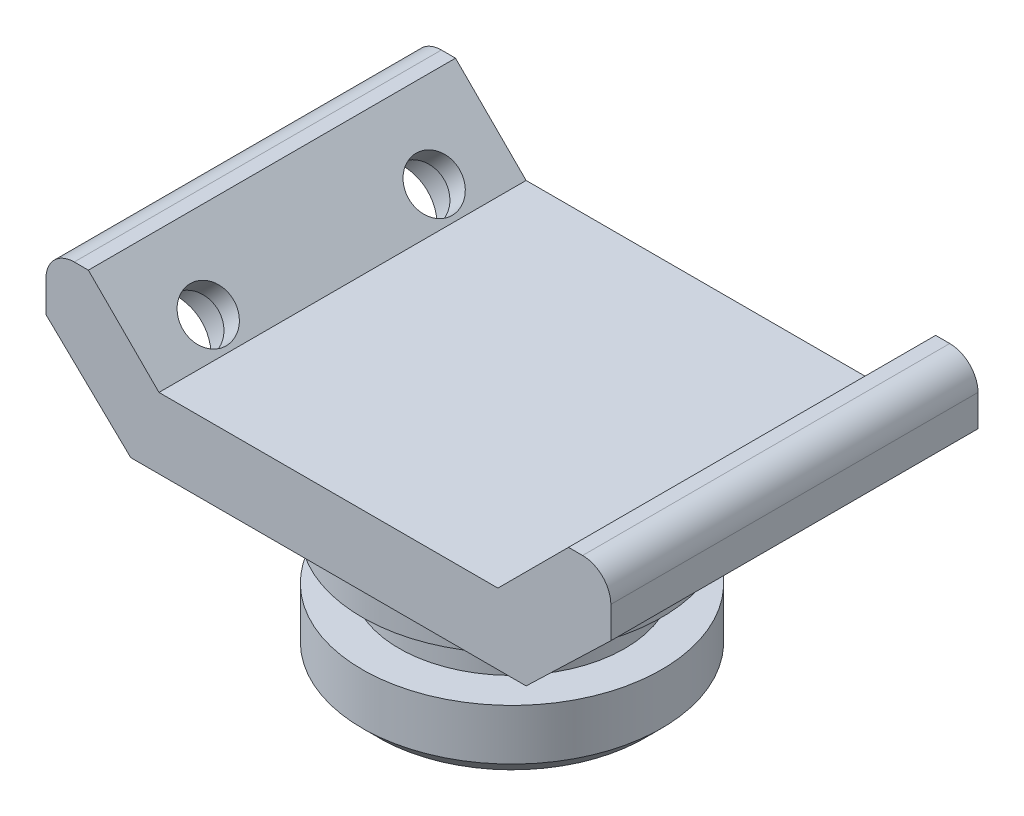
SolidWorks part; units mm, degrees
ref_plane "Alzado" through (0, 0, 0) normal (0, 0, 1) x (1, 0, 0)
ref_plane "Planta" through (0, 0, 0) normal (0, 1, 0) x (1, 0, 0)
ref_plane "Vista lateral" through (0, 0, 0) normal (1, 0, 0) x (0, 0, -1)
sketch "Sketch1" plane through (0, 0, 0) normal (0, 0, 1) x (1, 0, 0)
  line L0 (0, 0) -> (0, 47.9033) construction
  line L1 (-35, 0) -> (35, 0)
  line L2 (35, 0) -> (50, 14.4247)
  line L3 (50, 14.4247) -> (50, 25)
  line L4 (50, 25) -> (42.5, 25)
  line L5 (42.5, 25) -> (30, 12.5)
  line L6 (30, 12.5) -> (-30, 12.5)
  line L7 (-42.5, 25) -> (-30, 12.5)
  line L8 (-50, 25) -> (-42.5, 25)
  line L9 (-50, 14.4247) -> (-50, 25)
  line L10 (-35, 0) -> (-50, 14.4247)
  point P10 (0, 12.5)
  dimension "D1" = 25
  dimension "D2" = 15
  dimension "D3" = 12.5
  dimension "D4" = 12.5
  dimension "D5" = 30
  dimension "D6" = 50
extrude "Boss-Extrude1" add sketch "Sketch1" along normal mid plane 65
sketch "Sketch2" plane through (0, 0, 0) normal (0, 0, 1) x (1, 0, 0)
  line L0 (23.5, -30) -> (26.5, -27)
  line L1 (0, 0) -> (26.5, 0)
  line L2 (0, 0) -> (0, -30)
  line L3 (0, -30) -> (23.5, -30)
  line L4 (26.5, 0) -> (26.5, -10)
  line L8 (26.5, -18) -> (26.5, -27)
  line L9 (26.5, -10) -> (20, -10)
  line L10 (26.5, -18) -> (20, -18)
  line L11 (20, -10) -> (20, -18)
  point P1 (26.5, -30)
  dimension "D1" = 30
  dimension "D2" = 8
  dimension "D3" = 10
  dimension "D4" = 26.5
  dimension "D5" = 20
revolve "Revolve1" add sketch "Sketch2" angle 360 about L2
sketch "Sketch3" plane through (16.816, -17.4866, 0) normal (0.6931, -0.7208, 0) x (0.7208, 0.6931, 0)
  line L0 (35.633, 32.5) -> (35.633, -32.5) construction
  line L1 (25.2278, 32.5) -> (46.0382, 32.5) construction
  line L2 (25.2278, -32.5) -> (46.0382, -32.5) construction
  line L3 (46.0382, 0) -> (25.2278, 0) construction
  line L4 (46.0382, 32.5) -> (46.0382, -32.5) construction
  line L5 (25.2278, 32.5) -> (25.2278, -32.5) construction
  point P12 (35.633, 20)
  point P13 (35.633, -20)
  dimension "D1" = 40
hole_wizard "CBORE for M8 Hex Socket Head Cap Screw1" positions "Sketch5" profile "Sketch4" counterbore size "M8" standard "ISO" end condition through all
sketch "Sketch5" plane through (16.816, -17.4866, 0) normal (0.6931, -0.7208, 0) x (-0.7208, -0.6931, 0)
  point P0 (-35.633, -20)
  point P3 (-35.633, 20)
sketch "Sketch4" plane through (42.5, 7.2124, 20) normal (0, 0, 1) x (0.7208, 0.6931, 0)
  line L0 (0, 0) -> (0, 76.9375)
  line L1 (0, 76.9375) -> (4.5, 76.9375)
  line L3 (4.5, 76.9375) -> (4.5, 8.6)
  line L4 (4.5, 8.6) -> (7.5, 8.6)
  line L5 (7.5, 8.6) -> (7.5, 0)
  line L7 (7.5, 0) -> (0, 0)
  line L11 (0, -6.35) -> (0, 107.95) construction
  dimension "Thru Hole Dia." = 9
  dimension "Thru Hole Depth" = 76.9375
  dimension "C'Bore Dia." = 15
  dimension "C'Bore Depth" = 8.6
mirror "Mirror1" about plane through (0, 0, 0) normal (1, 0, 0) of "CBORE for M8 Hex Socket Head Cap Screw1"
fillet "Fillet1" radius 5 2 edges at (-50, 25, 0) (50, 25, 0)
